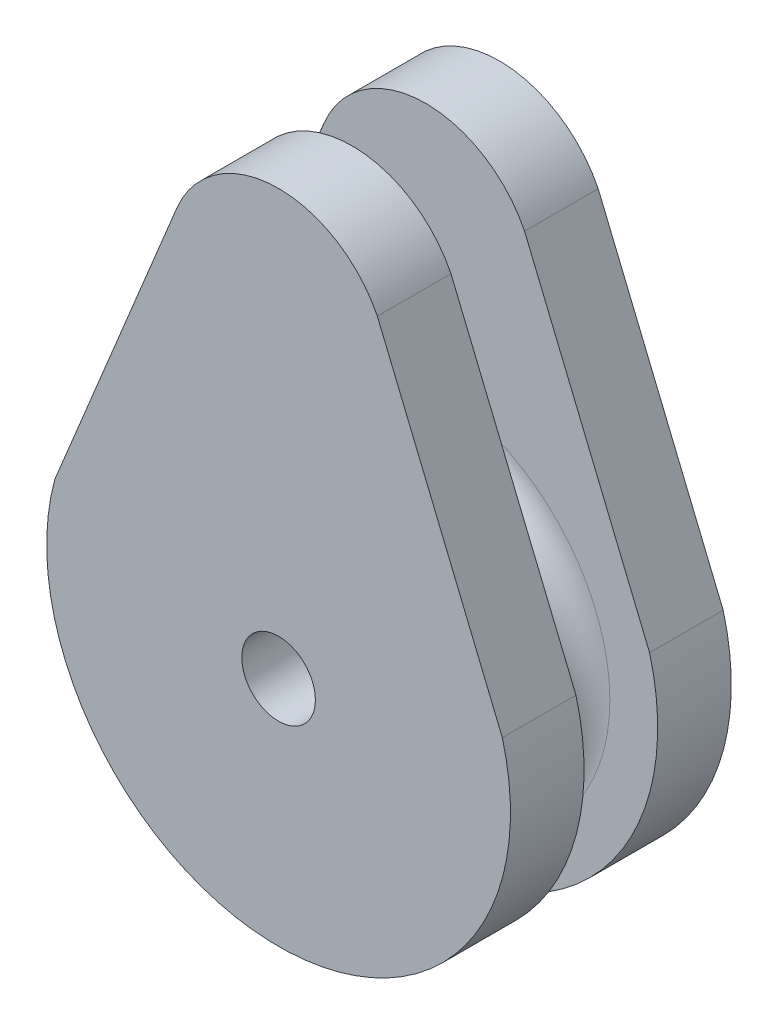
SolidWorks part; units mm, degrees
ref_plane "Front Plane" through (0, 0, 0) normal (0, 0, 1) x (1, 0, 0)
ref_plane "Top Plane" through (0, 0, 0) normal (0, 1, 0) x (1, 0, 0)
ref_plane "Right Plane" through (0, 0, 0) normal (1, 0, 0) x (0, 0, -1)
sketch "草图1" plane through (0, 0, 0) normal (0, 0, 1) x (1, 0, 0)
  line L0 (0, -10) -> (0, 23.0689)
  line L1 (0, 23.0689) -> (0, 21.0689)
  line L2 (0, 0) -> (-12.1588, 3.3051)
  line L3 (-12.1588, 3.3051) -> (-5.5358, 19.3706)
  line L4 (-5.5358, 19.3706) -> (5.3669, 19.7435)
  line L5 (5.3669, 19.7435) -> (12.1588, 3.3051)
  line L6 (12.1588, 3.3051) -> (0, 0)
  circle A0 centre (0, 0) radius 10
  circle A1 centre (0, 0) radius 12.6
  circle A2 centre (0, 17.0885) radius 5.9877
extrude "凸台-拉伸1" add sketch "草图1" along normal blind 4
sketch "草图2" plane through (0, 0, 4) normal (0, 0, 1) x (1, 0, 0)
  circle A0 centre (0, 0) radius 8
extrude "凸台-拉伸2" add sketch "草图2" along normal blind 4
ref_plane "基准面1" through (0, 0, 6) normal (0, 0, 1) x (1, 0, 0)
mirror "镜向1" about plane through (0, 0, 6) normal (0, 0, 1) of "凸台-拉伸1"
sketch "草图4" plane through (0, 0, 6) normal (0, 0, 1) x (1, 0, 0)
  circle A0 centre (0, 0) radius 10
  circle A1 centre (0, 0) radius 8
sketch "草图9" plane through (0, 0, 0) normal (0, 1, 0) x (1, 0, 0)
  line L0 (0, 2.6576) -> (0, -14.6825)
sketch "草图10" plane through (0, 0, 8) normal (0, 0, -1) x (-1, 0, 0)
  circle A0 centre (0, 0) radius 10
sketch "草图12" plane through (0, 0, 0) normal (1, 0, 0) x (0, 0, -1)
  line L0 (-4, 19.7435) -> (-4, 3.3051) construction
  line L1 (-8, 8) -> (-4, 8)
  line L2 (-8, 8) -> (-8, 10)
  line L3 (-8, 10) -> (-4, 10)
  line L4 (-4, 8) -> (-4, 10)
revolve "旋转3" add sketch "草图12" angle 360 about L0
sketch "草图13" plane through (0, 0, 0) normal (1, 0, 0) x (0, 0, -1)
  line L0 (-4, 10) -> (-8, 10) construction
  circle A0 centre (-6, 10) radius 2
revolve "切除-旋转1" cut sketch "草图13" angle 360 about L0
sketch "草图14" plane through (0, 0, 0) normal (0, 0, -1) x (-1, 0, 0)
  circle A0 centre (0, 0) radius 2
extrude "切除-拉伸1" cut sketch "草图14" against normal blind 1
sketch "草图15" plane through (0, 0, 12) normal (0, 0, 1) x (1, 0, 0)
  circle A0 centre (0, 0) radius 2
extrude "切除-拉伸2" cut sketch "草图15" against normal through all
sketch "草图16" plane through (0, 0, 12) normal (0, 0, 1) x (1, 0, 0)
  line L0 (-0.2047, 23.0727) -> (0, -12.6)
  arc A0 (5.3669, 19.7435) -> (-5.5358, 19.3706) centre (0, 17.0885) ccw construction
  arc A1 (-12.1588, 3.3051) -> (12.1588, 3.3051) centre (0, 0) ccw construction
